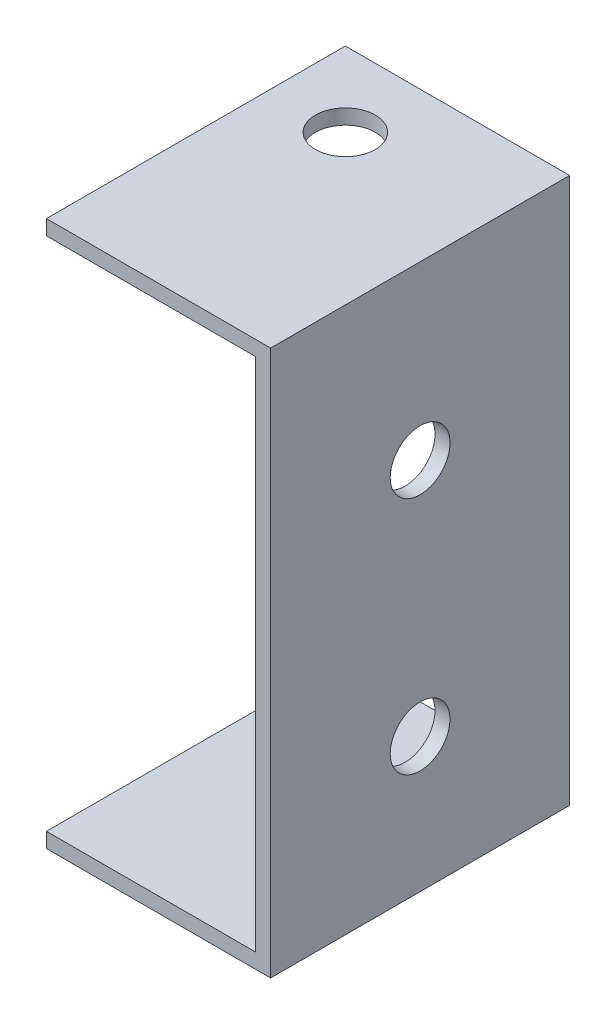
SolidWorks part; units mm, degrees
ref_plane "前视基准面" through (0, 0, 0) normal (0, 0, 1) x (1, 0, 0)
ref_plane "上视基准面" through (0, 0, 0) normal (0, 1, 0) x (1, 0, 0)
ref_plane "右视基准面" through (0, 0, 0) normal (1, 0, 0) x (0, 0, -1)
sketch "草图1" plane through (0, 0, 0) normal (0, 0, 1) x (1, 0, 0)
  line L0 (-61.1658, 46.995) -> (-31.1658, 46.995)
  line L1 (-31.1658, 46.995) -> (-31.1658, -26.005)
  line L2 (-31.1658, -26.005) -> (-61.1658, -26.005)
  line L3 (-61.1658, -26.005) -> (-61.1658, -24.005)
  line L4 (-61.1658, -24.005) -> (-33.1658, -24.005)
  line L5 (-33.1658, -24.005) -> (-33.1658, 44.995)
  line L6 (-33.1658, 44.995) -> (-61.1658, 44.995)
  line L7 (-61.1658, 44.995) -> (-61.1658, 46.995)
  dimension "D1" = 30
  dimension "D2" = 73
  dimension "D3" = 2
  dimension "D4" = 28
  dimension "D5" = 69
extrude "凸台-拉伸1" add sketch "草图1" along normal blind 40
sketch "草图3" plane through (-33.1658, 0, 0) normal (-1, 0, 0) x (0, 0, 1)
  line L0 (20, 44.995) -> (20, -24.005) construction
  line L1 (40, 44.995) -> (0, 44.995) construction
  line L2 (40, -24.005) -> (0, -24.005) construction
  line L3 (20, -24.005) -> (20, -8.005) construction
  line L4 (20, -8.005) -> (20, 23.995) construction
  circle A0 centre (20, 23.995) radius 4
  circle A1 centre (20, -8.005) radius 4
  dimension "D3" = 8
  dimension "D4" = 8
  dimension "D1" = 16
  dimension "D2" = 32
extrude "切除-拉伸1" cut sketch "草图3" against normal blind 40
sketch "草图4" plane through (0, 46.995, 0) normal (0, 1, 0) x (1, 0, 0)
  line L0 (-61.1658, -20) -> (-51.1658, -20) construction
  line L3 (-61.1658, -40) -> (-61.1658, 0) construction
  line L4 (-51.1658, -20) -> (-51.1658, -10) construction
  circle A3 centre (-51.1658, -10) radius 4
  dimension "D1" = 10
  dimension "D2" = 10
  dimension "D3" = 8
extrude "切除-拉伸2" cut sketch "草图4" against normal blind 96
